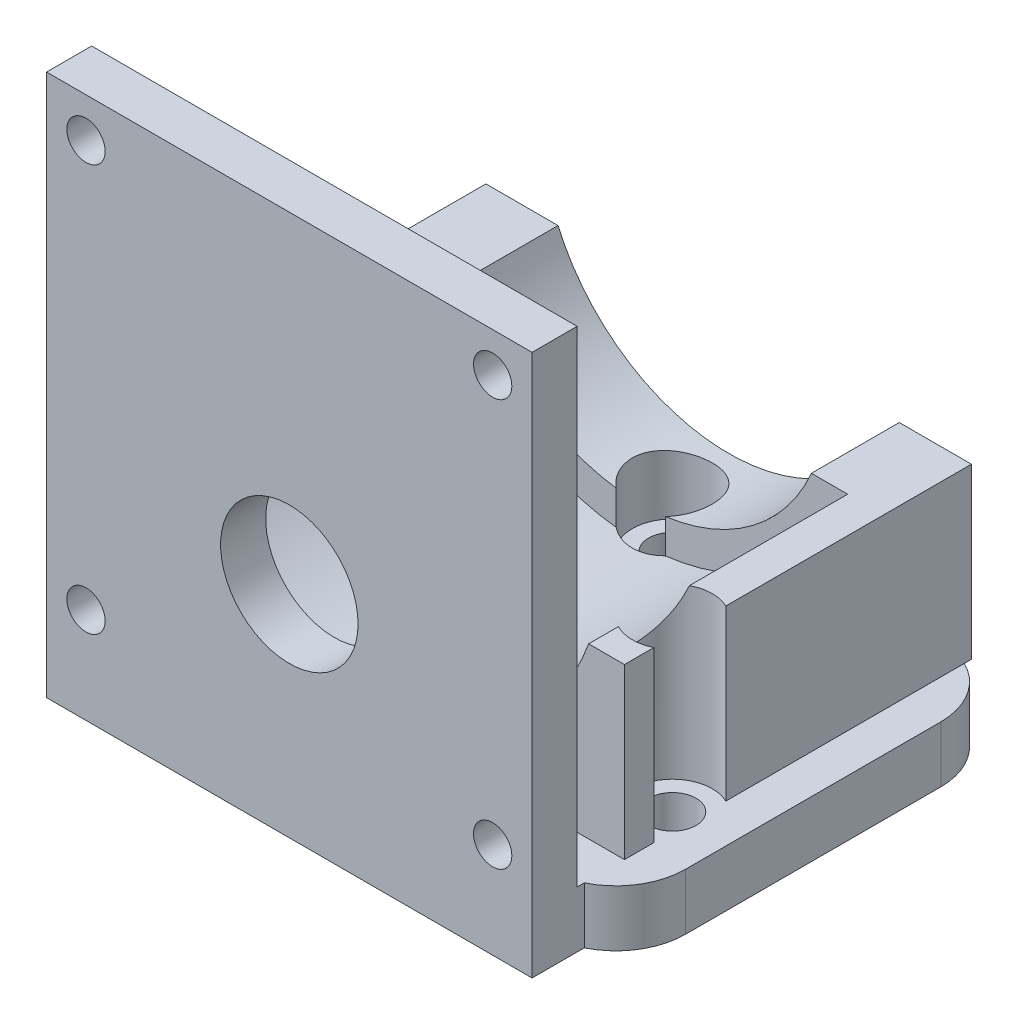
SolidWorks part; units mm, degrees
ref_plane "정면" through (0, 0, 0) normal (0, 0, 1) x (1, 0, 0)
ref_plane "윗면" through (0, 0, 0) normal (0, 1, 0) x (1, 0, 0)
ref_plane "우측면" through (0, 0, 0) normal (1, 0, 0) x (0, 0, -1)
sketch "스케치1" plane through (0, 0, 0) normal (0, 0, 1) x (1, 0, 0)
  line L1 (-15, 15) -> (15, 15)
  line L2 (-15, 15) -> (-15, -15)
  line L3 (-15, -15) -> (15, -15)
  line L4 (15, 15) -> (15, -15)
  line L5 (-15, 15) -> (15, -15) construction
  line L6 (-15, -15) -> (15, 15) construction
  point P4 (0, 0)
  dimension "D1" = 30
  dimension "D2" = 30
extrude "보스-돌출1" add sketch "스케치1" along normal blind 5 contours L1 L4 L3 L2
sketch "스케치2" plane through (0, 0, 0) normal (0, 0, -1) x (-1, 0, 0)
  line L0 (15, 15) -> (15, -15) construction
  line L1 (-15, -15) -> (15, -15)
  line L2 (-15, -15) -> (-15, -10)
  line L3 (-15, -10) -> (15, -10)
  line L4 (15, -15) -> (15, -10)
  line L5 (-15, -15) -> (15, -10) construction
  line L6 (-15, -10) -> (15, -15) construction
  point P4 (0, -12.5)
  dimension "D1" = 5
extrude "보스-돌출2" add sketch "스케치2" along normal blind 10
sketch "스케치3" plane through (0, -10, 0) normal (0, 1, 0) x (1, 0, 0)
  line L0 (-15, 10) -> (15, 10) construction
  circle A0 centre (0, 5) radius 2.1
  point P6 (0, 10)
  dimension "D1" = 4.2
  dimension "D2" = 5
extrude "컷-돌출1" cut sketch "스케치3" against normal blind 5
sketch "스케치4" plane through (0, 0, 5) normal (0, 0, 1) x (1, 0, 0)
  line L0 (10.2, -15) -> (15, -15)
  line L1 (-15, -15) -> (-10.2, -15)
  line L2 (-15, -15) -> (-15, 15)
  line L3 (-15, 15) -> (15, 15)
  line L4 (15, -15) -> (15, 15)
  line L5 (-15, -15) -> (15, 15) construction
  line L6 (-15, 15) -> (15, -15) construction
  line L8 (-10.2, -15) -> (-10.2, -18.9972)
  line L9 (-10.2, -18.9972) -> (10.2, -18.9972)
  line L10 (10.2, -15) -> (10.2, -18.9972)
  line L11 (-10.2, -15) -> (10.2, -18.9972) construction
  line L12 (-10.2, -18.9972) -> (10.2, -15) construction
  point P4 (0, 0)
  point P11 (0, -16.9986)
  dimension "D1" = 4.8
  dimension "D2" = 4.8
  dimension "D3" = 3.9972
extrude "보스-돌출3" add sketch "스케치4" along normal blind 20
sketch "스케치5" plane through (-15, 0, 0) normal (-1, 0, 0) x (0, 0, 1)
  line L0 (25, 15) -> (25, -15) construction
  line L1 (-10, -15) -> (25, -15)
  line L2 (-10, -15) -> (-10, -10)
  line L3 (-10, -10) -> (25, -10)
  line L4 (25, -15) -> (25, -10)
  line L5 (-10, -15) -> (25, -10) construction
  line L6 (-10, -10) -> (25, -15) construction
  point P4 (7.5, -12.5)
  dimension "D1" = 5
extrude "보스-돌출4" add sketch "스케치5" along normal blind 10
sketch "스케치6" plane through (15, 0, 0) normal (1, 0, 0) x (0, 0, -1)
  line L1 (-25, -15) -> (10, -15)
  line L2 (-25, -15) -> (-25, -10)
  line L3 (-25, -10) -> (10, -10)
  line L4 (10, -15) -> (10, -10)
  line L5 (-25, -15) -> (10, -10) construction
  line L6 (-25, -10) -> (10, -15) construction
  point P4 (-7.5, -12.5)
extrude "보스-돌출5" add sketch "스케치6" along normal blind 10
sketch "스케치7" plane through (0, -10, 0) normal (0, 1, 0) x (1, 0, 0)
  line L0 (-25, -25) -> (-25, 10) construction
  line L1 (25, 10) -> (25, -25) construction
  line L2 (-25, -25) -> (-15, -25) construction
  circle A0 centre (-20, -15) radius 2.1
  circle A1 centre (20, -15) radius 2.1
  dimension "D1" = 4.2
  dimension "D2" = 5
  dimension "D3" = 5
  dimension "D4" = 10
extrude "컷-돌출2" cut sketch "스케치7" against normal blind 10
fillet "필렛1" radius 6.17 1 edges at (25, -12.5, 25)
fillet "필렛2" radius 6.17 1 edges at (25, -12.5, -10)
sketch "스케치8" plane through (0, 15, 0) normal (0, 1, 0) x (1, 0, 0)
  line L1 (-22.1246, 5.0263) -> (20.9688, 5.0263)
  line L2 (-22.1246, 5.0263) -> (-22.1246, -26.7297)
  line L3 (-22.1246, -26.7297) -> (20.9688, -26.7297)
  line L4 (20.9688, 5.0263) -> (20.9688, -26.7297)
  line L5 (-22.1246, 5.0263) -> (20.9688, -26.7297) construction
  line L6 (-22.1246, -26.7297) -> (20.9688, 5.0263) construction
  point P4 (-0.5779, -10.8517)
extrude "컷-돌출3" cut sketch "스케치8" against normal up to vertex (25 mm away)
ref_plane "평면1" through (0, -10, 0) normal (0, 1, 0) x (1, 0, 0)
ref_plane "평면2" through (0, 0, 29) normal (0, 0, 1) x (1, 0, 0)
sketch "스케치9" plane through (0, 0, 29) normal (0, 0, 1) x (1, 0, 0)
  line L0 (19.25, -10) -> (-19.25, -10) construction
  line L1 (-21.55, 33.1) -> (21.55, 33.1)
  line L2 (-21.55, 33.1) -> (-21.55, -10)
  line L3 (-21.55, -10) -> (21.55, -10)
  line L4 (21.55, 33.1) -> (21.55, -10)
  line L5 (-21.55, 33.1) -> (21.55, -10) construction
  line L6 (-21.55, -10) -> (21.55, 33.1) construction
  line L7 (-25, -15) -> (-25, -10) construction
  circle A0 centre (0, 4.5) radius 6.1
  circle A1 centre (18.05, 29.6) radius 1.7
  circle A2 centre (18.05, -6.5) radius 1.7
  circle A3 centre (-18.05, -6.5) radius 1.7
  circle A4 centre (-18.05, 29.6) radius 1.7
  point P4 (0, 11.55)
  point P9 (0, 0)
  point P12 (0, 0)
  point P20 (0, 11.55)
  point P22 (0, 0)
  point P23 (0, 0)
  point P24 (0, 0)
  dimension "D3" = 12.2
  dimension "D4" = 3.4
  dimension "D1" = 43.1
  dimension "D2" = 43.1
  dimension "D5" = 3.5
  dimension "D6" = 14.5
  dimension "D8" = 3.45
  dimension "D7" = 4
extrude "보스-돌출6" add sketch "스케치9" against normal blind 4 separate body
ref_plane "평면3" through (0, 0, 20.8) normal (0, 0, -1) x (-1, 0, 0)
sketch "스케치10" plane through (0, 0, 20.8) normal (0, 0, -1) x (-1, 0, 0)
  line L0 (-21.55, -10) -> (-21.55, 33.1) construction
  line L1 (-21.55, 5) -> (-18.367, 5)
  line L2 (-21.55, 5) -> (-21.55, -10)
  line L3 (-21.55, -10) -> (21.55, -10)
  line L4 (21.55, 5) -> (21.55, -10)
  line L5 (-21.55, 5) -> (21.55, -10) construction
  line L6 (-21.55, -10) -> (21.55, 5) construction
  line L7 (19.25, -10) -> (-19.25, -10) construction
  line L8 (21.55, 33.1) -> (21.55, -10) construction
  line L9 (18.367, 5) -> (21.55, 5)
  arc A0 (-18.367, 5) -> (18.367, 5) centre (0, 11.55) ccw
  point P6 (0, -2.5)
  point P14 (0, 0)
  dimension "D1" = 39
  dimension "D2" = 15
extrude "보스-돌출7" add sketch "스케치10" along normal blind 23 separate body
sketch "스케치11" plane through (0, 0, -2.2) normal (0, 0, -1) x (-1, 0, 0)
  line L0 (19.25, -10) -> (-19.25, -10) construction
  line L1 (-21.55, 5) -> (-15.1442, 5)
  line L2 (-21.55, 5) -> (-21.55, -10)
  line L3 (-21.55, -10) -> (21.55, -10)
  line L4 (21.55, 5) -> (21.55, -10)
  line L5 (-21.55, 5) -> (21.55, -10) construction
  line L6 (-21.55, -10) -> (21.55, 5) construction
  line L7 (21.55, -10) -> (21.55, 5) construction
  line L8 (15.1442, 5) -> (21.55, 5)
  arc A0 (-15.1442, 5) -> (15.1442, 5) centre (0, 11.55) ccw
  arc A1 (-18.367, 5) -> (18.367, 5) centre (0, 11.55) ccw construction
  point P6 (0, -2.5)
  dimension "D1" = 33
extrude "보스-돌출8" add sketch "스케치11" along normal up to vertex (7.8 mm away)
sketch "스케치12" plane through (0, 0, 25) normal (0, 0, 1) x (1, 0, 0)
  line L1 (-25, -15) -> (26.859, -15)
  line L2 (-25, -15) -> (-25, -24.121)
  line L3 (-25, -24.121) -> (26.859, -24.121)
  line L4 (26.859, -15) -> (26.859, -24.121)
  line L5 (-25, -15) -> (26.859, -24.121) construction
  line L6 (-25, -24.121) -> (26.859, -15) construction
  point P4 (0.9295, -19.5605)
extrude "컷-돌출4" cut sketch "스케치12" against normal up to vertex
sketch "스케치14" plane through (0, 0, 29) normal (0, 0, 1) x (1, 0, 0)
  line L0 (19.25, -10) -> (-19.25, -10) construction
  line L1 (-21.55, -10) -> (21.55, -10)
  line L2 (-21.55, -10) -> (-21.55, -15)
  line L3 (-21.55, -15) -> (21.55, -15)
  line L4 (21.55, -10) -> (21.55, -15)
  line L5 (-21.55, -10) -> (21.55, -15) construction
  line L6 (-21.55, -15) -> (21.55, -10) construction
  line L7 (-21.55, 33.1) -> (-21.55, -10) construction
  line L8 (21.55, -10) -> (21.55, 33.1) construction
  line L9 (-25, -15) -> (18.83, -15) construction
  point P4 (0, -12.5)
extrude "보스-돌출9" add sketch "스케치14" against normal up to vertex (8.2 mm away)
sketch "스케치15" plane through (0, -15, 0) normal (0, -1, 0) x (1, 0, 0)
  line L0 (-20, 15) -> (20, 15) construction
  line L1 (0, -5) -> (0, 15) construction
  line L2 (0, -5) -> (0, 35) construction
  line L3 (20, 15) -> (-20, 15) construction
  line L4 (0, 15) -> (-20, 15) construction
  line L5 (0, 15) -> (0, -5) construction
  circle A0 centre (-20, 15) radius 2.1
  arc A1 (-21.55, 13.5831) -> (-21.55, 16.4169) centre (-20, 15) ccw construction
  circle A2 centre (0, -5) radius 2.1
  circle A3 centre (20, 15) radius 2.1
  dimension "D2" = 90
  dimension "D1" = 3
extrude "컷-돌출5" cut sketch "스케치15" against normal through all
sketch "스케치16" plane through (0, -10, 0) normal (0, 1, 0) x (1, 0, 0)
  line L0 (-20, -15) -> (20, -15) construction
  line L1 (0, 5) -> (0, -15) construction
  line L3 (0, -15) -> (20, -15) construction
  line L4 (0, -15) -> (0, 5) construction
  circle A0 centre (20, -15) radius 3.55
  circle A4 centre (0, 5) radius 3.55
  circle A5 centre (-20, -15) radius 3.55
  dimension "D1" = 7.1
  dimension "D3" = 90
  dimension "D2" = 3
extrude "컷-돌출6" cut sketch "스케치16" along normal through all
